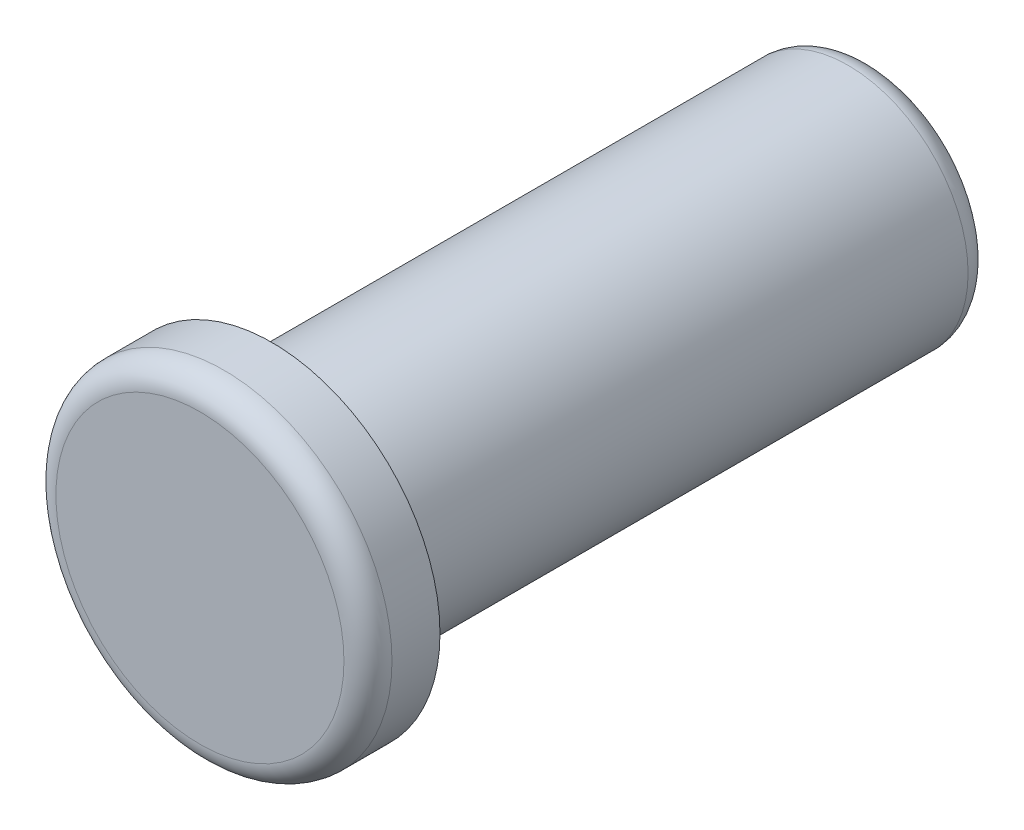
SolidWorks part; units mm, degrees
ref_plane "Přední rovina" through (0, 0, 0) normal (0, 0, 1) x (1, 0, 0)
ref_plane "Vrchní rovina" through (0, 0, 0) normal (0, 1, 0) x (1, 0, 0)
ref_plane "Pravá rovina" through (0, 0, 0) normal (1, 0, 0) x (0, 0, -1)
sketch "Skica1" plane through (0, 0, 0) normal (0, 0, 1) x (1, 0, 0)
  circle A0 centre (0, 0) radius 7
  dimension "D1" = 14
extrude "Přidat vysunutím1" add sketch "Skica1" along normal blind 3
sketch "Skica2" plane through (0, 0, 0) normal (0, 0, -1) x (-1, 0, 0)
  circle A0 centre (0, 0) radius 5
  dimension "D1" = 10
extrude "Přidat vysunutím2" add sketch "Skica2" along normal blind 25
fillet "Zaoblit1" radius 1 2 edges at (7, 0, 3) (-5, 0, -25)
